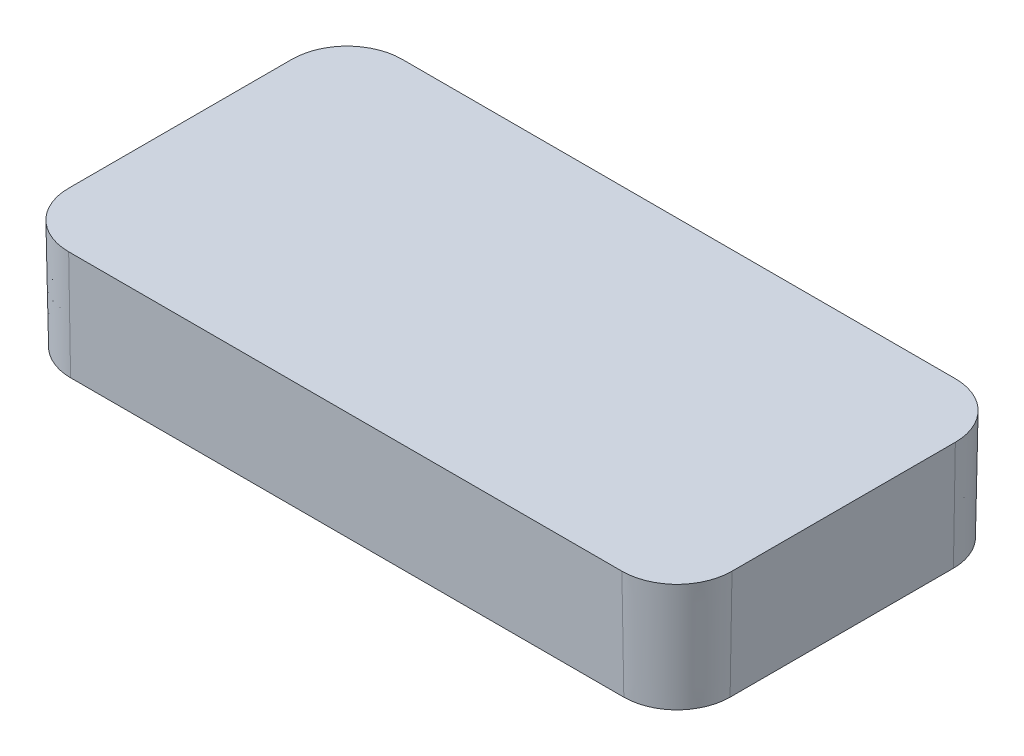
SolidWorks part; units mm, degrees
material "CA"
ref_plane "Front Plane" through (0, 0, 0) normal (0, 0, 1) x (1, 0, 0)
ref_plane "Top Plane" through (0, 0, 0) normal (0, 1, 0) x (1, 0, 0)
ref_plane "Right Plane" through (0, 0, 0) normal (1, 0, 0) x (0, 0, -1)
sketch "Sketch1" plane through (0, 0, 0) normal (0, 1, 0) x (1, 0, 0)
  line L1 (-15.9512, -9.6139) -> (15.9512, -9.6139)
  line L2 (-19.1262, -6.4389) -> (-19.1262, 6.4389)
  line L3 (-15.9512, 9.6139) -> (15.9512, 9.6139)
  line L4 (19.1262, -6.4389) -> (19.1262, 6.4389)
  line L5 (-19.1262, -9.6139) -> (19.1262, 9.6139) construction
  line L6 (-19.1262, 9.6139) -> (19.1262, -9.6139) construction
  arc A0 (-15.9512, -9.6139) -> (-19.1262, -6.4389) centre (-15.9512, -6.4389) cw
  arc A1 (15.9512, -9.6139) -> (19.1262, -6.4389) centre (15.9512, -6.4389) ccw
  arc A2 (15.9512, 9.6139) -> (19.1262, 6.4389) centre (15.9512, 6.4389) cw
  arc A3 (-19.1262, 6.4389) -> (-15.9512, 9.6139) centre (-15.9512, 6.4389) cw
  point P0 (0, 0)
  dimension "D3" = 3.175
  dimension "D1" = 38.2524
  dimension "D2" = 19.2278
extrude "Boss-Extrude1" add sketch "Sketch1" against normal blind 2.3622 draft 1
sketch "Sketch7" plane through (0, 0, 0) normal (0, 1, 0) x (1, 0, 0)
  line L4 (-15.9512, -9.6139) -> (15.9512, -9.6139)
  line L5 (19.1262, -6.4389) -> (19.1262, 6.4389)
  line L6 (15.9512, 9.6139) -> (-15.9512, 9.6139)
  line L7 (-19.1262, 6.4389) -> (-19.1262, -6.4389)
  line L8 (-15.9512, -9.6139) -> (15.9512, -9.6139)
  line L9 (19.1262, -6.4389) -> (19.1262, 6.4389)
  line L10 (15.9512, 9.6139) -> (-15.9512, 9.6139)
  line L11 (-19.1262, 6.4389) -> (-19.1262, -6.4389)
  line L20 (-15.9512, -7.8359) -> (15.9512, -7.8359)
  line L21 (17.3482, -6.4389) -> (17.3482, 6.4389)
  line L22 (15.9512, 7.8359) -> (-15.9512, 7.8359)
  line L23 (-17.3482, 6.4389) -> (-17.3482, -6.4389)
  line L24 (-15.9512, -7.8359) -> (15.9512, -7.8359)
  line L25 (17.3482, -6.4389) -> (17.3482, 6.4389)
  line L26 (15.9512, 7.8359) -> (-15.9512, 7.8359)
  line L27 (-17.3482, 6.4389) -> (-17.3482, -6.4389)
  arc A4 (-19.1262, -6.4389) -> (-15.9512, -9.6139) centre (-15.9512, -6.4389) ccw
  arc A5 (15.9512, -9.6139) -> (19.1262, -6.4389) centre (15.9512, -6.4389) ccw
  arc A6 (19.1262, 6.4389) -> (15.9512, 9.6139) centre (15.9512, 6.4389) ccw
  arc A7 (-15.9512, 9.6139) -> (-19.1262, 6.4389) centre (-15.9512, 6.4389) ccw
  arc A8 (-19.1262, -6.4389) -> (-15.9512, -9.6139) centre (-15.9512, -6.4389) ccw
  arc A9 (15.9512, -9.6139) -> (19.1262, -6.4389) centre (15.9512, -6.4389) ccw
  arc A10 (19.1262, 6.4389) -> (15.9512, 9.6139) centre (15.9512, 6.4389) ccw
  arc A11 (-15.9512, 9.6139) -> (-19.1262, 6.4389) centre (-15.9512, 6.4389) ccw
  arc A20 (-17.3482, -6.4389) -> (-15.9512, -7.8359) centre (-15.9512, -6.4389) ccw
  arc A21 (15.9512, -7.8359) -> (17.3482, -6.4389) centre (15.9512, -6.4389) ccw
  arc A22 (17.3482, 6.4389) -> (15.9512, 7.8359) centre (15.9512, 6.4389) ccw
  arc A23 (-15.9512, 7.8359) -> (-17.3482, 6.4389) centre (-15.9512, 6.4389) ccw
  arc A24 (-17.3482, -6.4389) -> (-15.9512, -7.8359) centre (-15.9512, -6.4389) ccw
  arc A25 (15.9512, -7.8359) -> (17.3482, -6.4389) centre (15.9512, -6.4389) ccw
  arc A26 (17.3482, 6.4389) -> (15.9512, 7.8359) centre (15.9512, 6.4389) ccw
  arc A27 (-15.9512, 7.8359) -> (-17.3482, 6.4389) centre (-15.9512, 6.4389) ccw
  dimension "D1" = 0
  dimension "D2" = 1.778
extrude "Boss-Extrude3" add sketch "Sketch7" against normal blind 6.35 draft 1
draft "Draft1" type of draft neutral plane draft angle 10 faces to draft 8 face at (-16.8403, -4.3561, -7.328) face at (0, -4.3561, -7.9119) face at (16.8403, -4.3561, -7.328) face at (17.4242, -4.3561, 0) face at (16.8403, -4.3561, 7.328) face at (-16.8403, -4.3561, 7.328) face at (0, -4.3561, 7.9119) face at (-17.4242, -4.3561, 0) neutral plane through (-15.9512, -2.3622, 6.4389) neutral plane normal (0, -1, 0) parameters "D1"=10
sketch "Sketch8" plane through (0, 0, 0) normal (0, 0, 1) x (1, 0, 0)
  line L0 (0, 0) -> (0, -11.7034) construction
  line L1 (15.9512, -2.3622) -> (-15.9512, -2.3622) construction
  line L2 (15.9512, -2.3622) -> (-15.9512, -2.3622) construction
  line L3 (0, -3.1559) -> (0.7938, -2.3622)
  line L4 (0, -3.1559) -> (-0.7937, -2.3622)
  line L5 (-0.7937, -2.3622) -> (0.7938, -2.3622)
  dimension "D1" = 90
  dimension "D2" = 1.5875
extrude "Boss-Extrude4" add sketch "Sketch8" along normal up to next and the other way up to next
pattern_linear "LPattern1" count 12 spacing 1.5875 along (1, 0, 0) count 12 spacing 1.5875 along (-1, 0, 0) of "Boss-Extrude4"
sketch "Sketch9" plane through (0, 0, 0) normal (1, 0, 0) x (0, 0, -1)
  line L0 (7.6853, -2.3622) -> (-7.6853, -2.3622) construction
  line L1 (0.7938, -2.3622) -> (-0.7937, -2.3622)
  line L2 (0, 0) -> (0, -3.1559) construction
  line L3 (-6.4389, 0) -> (6.4389, 0) construction
  line L4 (-0.7937, -2.3622) -> (0, -3.1559)
  line L5 (0.7938, -2.3622) -> (0, -3.1559)
  dimension "D1" = 90
  dimension "D2" = 1.5875
extrude "Boss-Extrude5" add sketch "Sketch9" along normal blind 17.78 and the other way blind 17.78
pattern_linear "LPattern2" count 6 spacing 1.5875 along (0, 0, 1) count 6 spacing 1.5875 along (0, 0, -1) of "Boss-Extrude5"
ref_plane "Plane1" through (0, -5.588, 0) normal (0, -1, 0) x (-1, 0, 0)
sketch "Sketch10" plane through (0, -5.588, 0) normal (0, -1, 0) x (-1, 0, 0)
  line L0 (17.4654, 7.9531) -> (16.4563, 6.944) construction
  line L1 (17.4654, 7.9531) -> (14.4991, 7.9531) construction
  arc A0 (18.0926, 6.4389) -> (15.9512, 8.5803) centre (15.9512, 6.4389) ccw construction
  arc A1 (18.0926, 6.4389) -> (15.9512, 8.5803) centre (15.9512, 6.4389) ccw construction
  circle A2 centre (17.1062, 7.5939) radius 1.1811
  dimension "D2" = 2.3622
  dimension "D1" = 45
  dimension "D3" = 0.508
extrude "Boss-Extrude6" add sketch "Sketch10" against normal through all
sketch "Sketch11" plane through (0, -5.588, 0) normal (0, -1, 0) x (1, 0, 0)
  circle A0 centre (-17.1062, -7.5939) radius 1.1811
extrude "Cut-Extrude1" cut sketch "Sketch11" along normal through all
mirror "Mirror1" about plane through (0, 0, 0) normal (1, 0, 0) of "Cut-Extrude1", "Boss-Extrude6"
mirror "Mirror2" about plane through (0, 0, 0) normal (0, 0, 1) of "Mirror1", "Boss-Extrude6", "Cut-Extrude1"
sketch "Sketch11 - OFFSET .005" plane through (0, 0, 0) normal (0, 1, 0) x (1, 0, 0)
  line L8 (-15.9512, -9.7409) -> (15.9512, -9.7409)
  line L9 (19.2532, -6.4389) -> (19.2532, 6.4389)
  line L10 (15.9512, 9.7409) -> (-15.9512, 9.7409)
  line L11 (-19.2532, 6.4389) -> (-19.2532, -6.4389)
  line L12 (-15.9512, -9.7409) -> (15.9512, -9.7409) construction
  line L13 (19.2532, -6.4389) -> (19.2532, 6.4389) construction
  line L14 (15.9512, 9.7409) -> (-15.9512, 9.7409) construction
  line L15 (-19.2532, 6.4389) -> (-19.2532, -6.4389) construction
  arc A8 (-19.2532, -6.4389) -> (-15.9512, -9.7409) centre (-15.9512, -6.4389) ccw
  arc A9 (15.9512, -9.7409) -> (19.2532, -6.4389) centre (15.9512, -6.4389) ccw
  arc A10 (19.2532, 6.4389) -> (15.9512, 9.7409) centre (15.9512, 6.4389) ccw
  arc A11 (-15.9512, 9.7409) -> (-19.2532, 6.4389) centre (-15.9512, 6.4389) ccw
  arc A12 (-19.2532, -6.4389) -> (-15.9512, -9.7409) centre (-15.9512, -6.4389) ccw construction
  arc A13 (15.9512, -9.7409) -> (19.2532, -6.4389) centre (15.9512, -6.4389) ccw construction
  arc A14 (19.2532, 6.4389) -> (15.9512, 9.7409) centre (15.9512, 6.4389) ccw construction
  arc A15 (-15.9512, 9.7409) -> (-19.2532, 6.4389) centre (-15.9512, 6.4389) ccw construction
  dimension "D1" = 0.127
